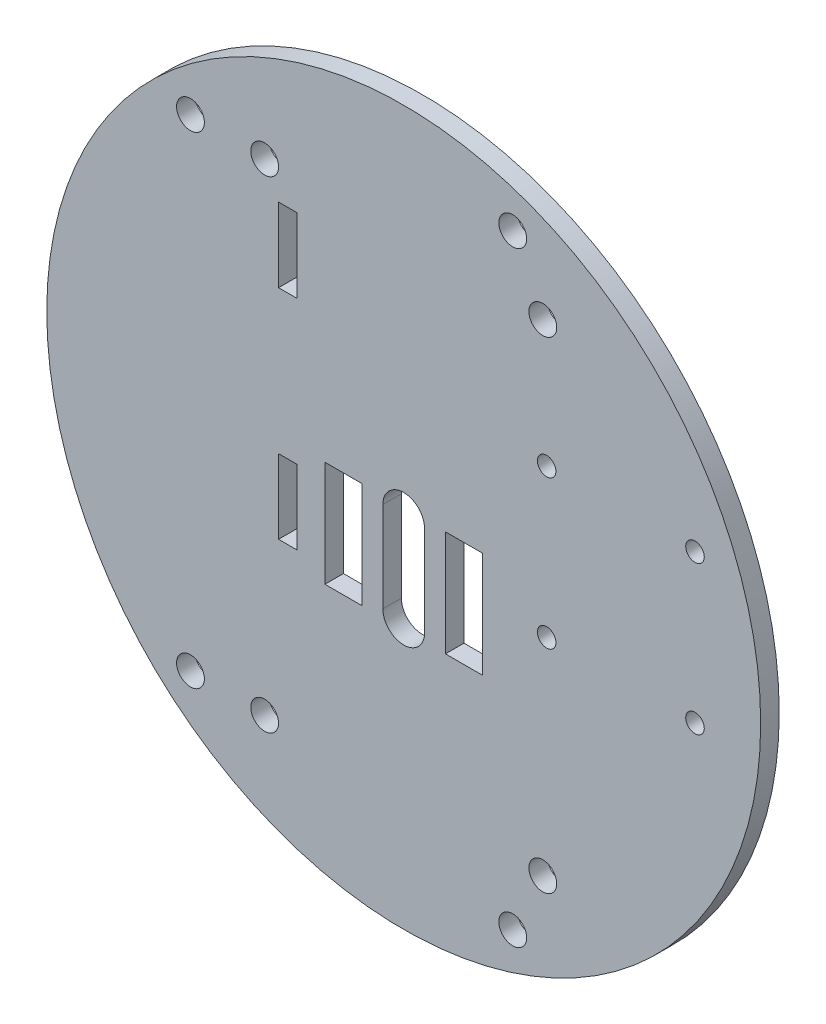
SolidWorks part; units mm, degrees
material "Acrylic (Medium-high impact)"
ref_plane "Front Plane" through (0, 0, 0) normal (0, 0, 1) x (1, 0, 0)
ref_plane "Top Plane" through (0, 0, 0) normal (0, 1, 0) x (1, 0, 0)
ref_plane "Right Plane" through (0, 0, 0) normal (1, 0, 0) x (0, 0, -1)
sketch "Model" plane through (0, 0, 0) normal (0, 0, 1) x (1, 0, 0)
  line L26 (-13.5, -8.8734) -> (-11.5, -8.8734)
  line L27 (-11.5, -8.8734) -> (-11.5, -0.8734)
  line L28 (-11.5, -0.8734) -> (-13.5, -0.8734)
  line L29 (-13.5, -0.8734) -> (-13.5, -8.8734)
  line L30 (-13.5, 14.6266) -> (-11.5, 14.6266)
  line L31 (-13.5, 14.6266) -> (-13.5, 22.6266)
  line L32 (-13.5, 22.6266) -> (-11.5, 22.6266)
  line L33 (-11.5, 22.6266) -> (-11.5, 14.6266)
  line L169 (-4.5, 0.8266) -> (-4.5, -10.5734)
  line L170 (4.5, 0.8266) -> (4.5, -10.5734)
  line L171 (-2.25, 0) -> (-2.25, -9.7468)
  line L172 (2.25, 0) -> (2.25, -9.7468)
  line L173 (4.5, 0.8266) -> (8.5, 0.8266)
  line L174 (4.5, -10.5734) -> (8.5, -10.5734)
  line L175 (8.5, -10.5734) -> (8.5, 0.8266)
  line L176 (-4.5, 0.8266) -> (-8.5, 0.8266)
  line L177 (-8.5, 0.8266) -> (-8.5, -10.5734)
  line L178 (-8.5, -10.5734) -> (-4.5, -10.5734)
  circle A71 centre (0, -0.0734) radius 38.5
  circle A72 centre (-23, 26.05) radius 1.5
  circle A73 centre (11.7571, -32.7195) radius 1.5
  circle A74 centre (11.7571, 32.5727) radius 1.5
  arc A75 (2.25, 0) -> (-2.25, 0) centre (0, 0) ccw
  arc A76 (-2.25, -9.7468) -> (2.25, -9.7468) centre (0, -9.7468) ccw
  circle A77 centre (31.4147, 12.4266) radius 1
  circle A78 centre (31.4147, -3.5734) radius 1
  circle A79 centre (15.4147, 12.4266) radius 1
  circle A80 centre (15.4147, -3.5734) radius 1
  circle A81 centre (-23, -25.91) radius 1.5
  circle A82 centre (-15, -26.0542) radius 1.5
  circle A83 centre (15, 25.9074) radius 1.5
  circle A84 centre (-15, 25.9074) radius 1.5
  circle A85 centre (15, -26.0542) radius 1.5
  dimension "D1" = 3
  dimension "D2" = 77
  dimension "D3" = 2
  dimension "D4" = 2.25
  dimension "D5" = 4.5
  dimension "D6" = 8.5
  dimension "D7" = 11.7571
  dimension "D8" = 15
  dimension "D9" = 15.4147
  dimension "D10" = 31.4147
  dimension "D11" = 4.5
  dimension "D12" = 15
  dimension "D13" = 23
  dimension "D14" = 0.8266
  dimension "D15" = 12.4266
  dimension "D16" = 26.05
  dimension "D17" = 25.9074
  dimension "D18" = 32.5727
  dimension "D19" = 0.0734
  dimension "D20" = 3.5734
  dimension "D21" = 9.7468
  dimension "D22" = 10.5734
  dimension "D23" = 25.91
  dimension "D24" = 26.0542
  dimension "D25" = 32.7195
  dimension "D29" = 8
  dimension "D33" = 15.5
  dimension "D35" = 1.7
  dimension "D36" = 3
  dimension "D37" = 2
extrude "Boss-Extrude1" add sketch "Model" along normal blind 2
